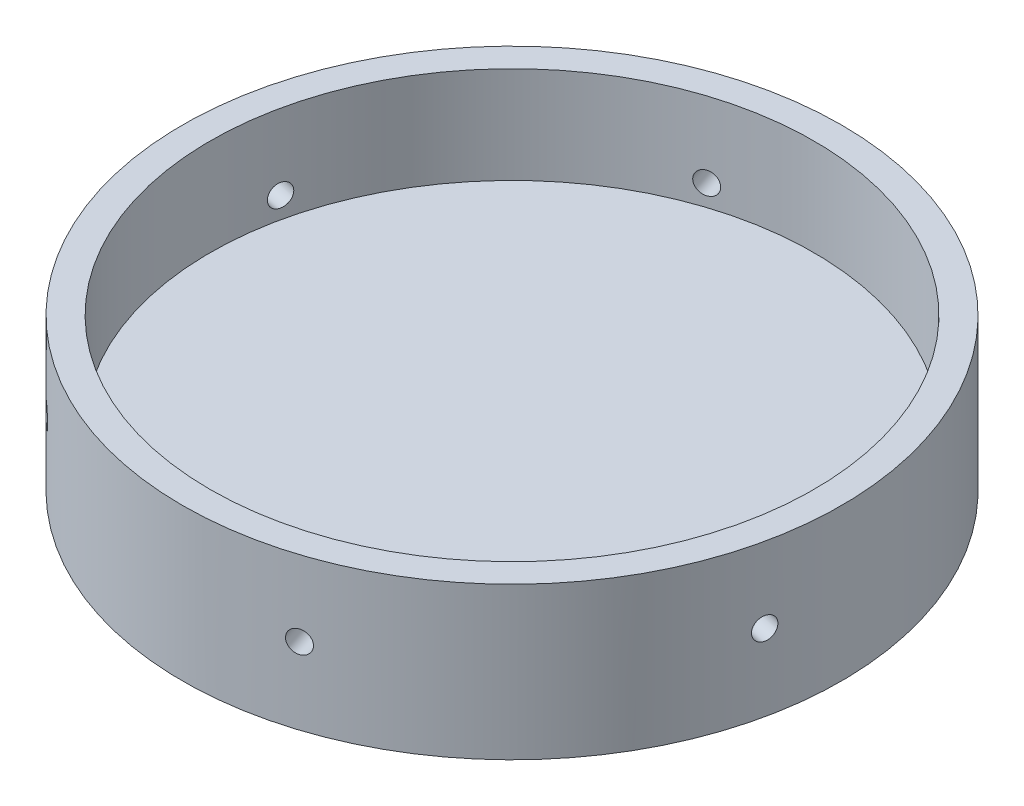
SolidWorks part; units mm, degrees
material "6061-T4 (SS)"
ref_plane "Front Plane" through (0, 0, 0) normal (0, 0, 1) x (1, 0, 0)
ref_plane "Top Plane" through (0, 0, 0) normal (0, 1, 0) x (1, 0, 0)
ref_plane "Right Plane" through (0, 0, 0) normal (1, 0, 0) x (0, 0, -1)
sketch "Sketch1" plane through (0, 0, 0) normal (0, 1, 0) x (1, 0, 0)
  circle A0 centre (0, 0) radius 75.692
  circle A1 centre (0, 0) radius 69.342
  dimension "D1" = 151.384
  dimension "D2" = 138.684
extrude "Boss-Extrude1" add sketch "Sketch1" along normal blind 22.225
sketch "Sketch2" plane through (0, 0, 0) normal (0, -1, 0) x (1, 0, 0)
  circle A0 centre (0, 0) radius 75.692
  dimension "D1" = 151.384
extrude "Boss-Extrude2" add sketch "Sketch2" along normal blind 12.7
hole_wizard "Tap Drill for 1/4-20 Tap1" positions "3DSketch2" profile "Sketch4" hole size "1/4-20" standard "ANSI Inch"
sketch3d "3DSketch2"
  line L0 (73.6526, 22.225, 17.4519) -> (73.9972, 4.8963, 15.9279)
  circle A1 centre (0, 22.225, 0) radius 75.692 construction
  point P0 (73.9972, 4.8963, 15.9279)
  point P10 (0, 97.917, 0)
  point P12 (-133.403, 50.4262, 0)
  dimension "D1" = 17.399
sketch "Sketch4" plane through (73.9972, 4.8963, 15.9279) normal (0, 1, 0) x (0.2104, 0, -0.9776)
  line L0 (0, 0) -> (0, 11.1858)
  line L1 (0, 11.1858) -> (2.5527, 9.652)
  line L2 (2.5527, 9.652) -> (2.5527, 0)
  line L5 (2.5527, 0) -> (0, 0)
  line L10 (0, 11.1858) -> (-2.5527, 9.652) construction
  line L11 (0, -6.35) -> (0, 107.95) construction
  dimension "Hole Dia." = 5.1054
  dimension "Hole Depth" = 9.652
  dimension "Drill Angle" = 118
pattern_circular "CirPattern1" count 6 over 360 about axis through (0, 22.225, 0) along (0, -1, 0) of "Tap Drill for 1/4-20 Tap1"
